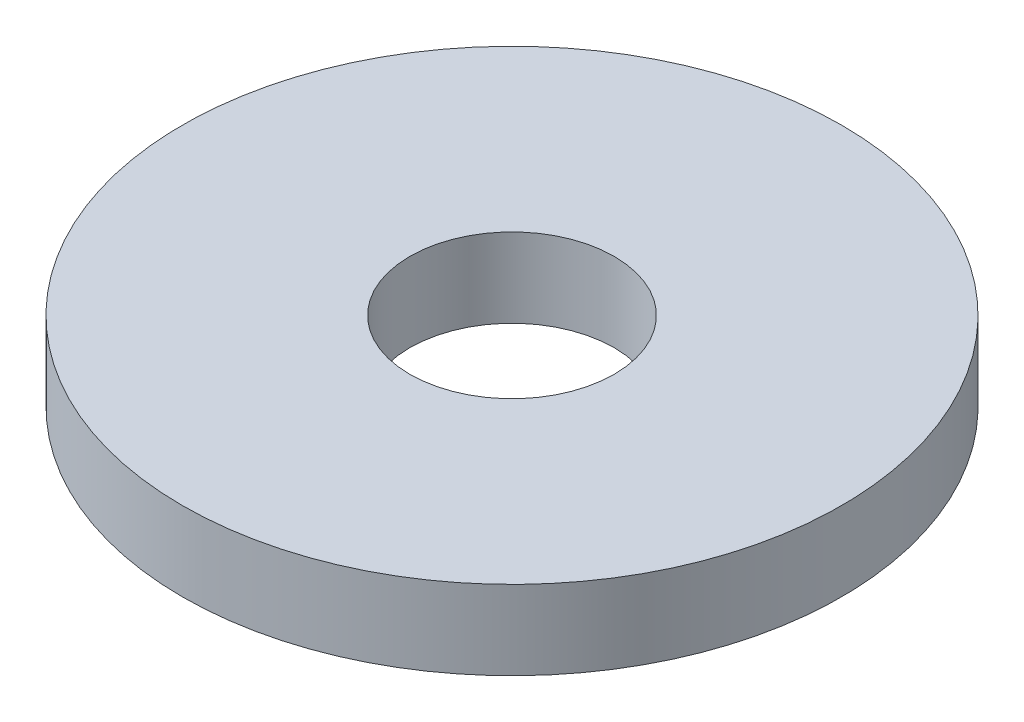
SolidWorks part; units mm, degrees
ref_plane "Alzado" through (0, 0, 0) normal (0, 0, 1) x (1, 0, 0)
ref_plane "Planta" through (0, 0, 0) normal (0, 1, 0) x (1, 0, 0)
ref_plane "Vista lateral" through (0, 0, 0) normal (1, 0, 0) x (0, 0, -1)
sketch "Sketch1" plane through (0, 0, 0) normal (0, 1, 0) x (1, 0, 0)
  circle A0 centre (0, 0) radius 5
  circle A1 centre (0, 0) radius 1.55
  dimension "D1" = 10
  dimension "D2" = 3.1
extrude "Boss-Extrude1" add sketch "Sketch1" along normal blind 1.2
